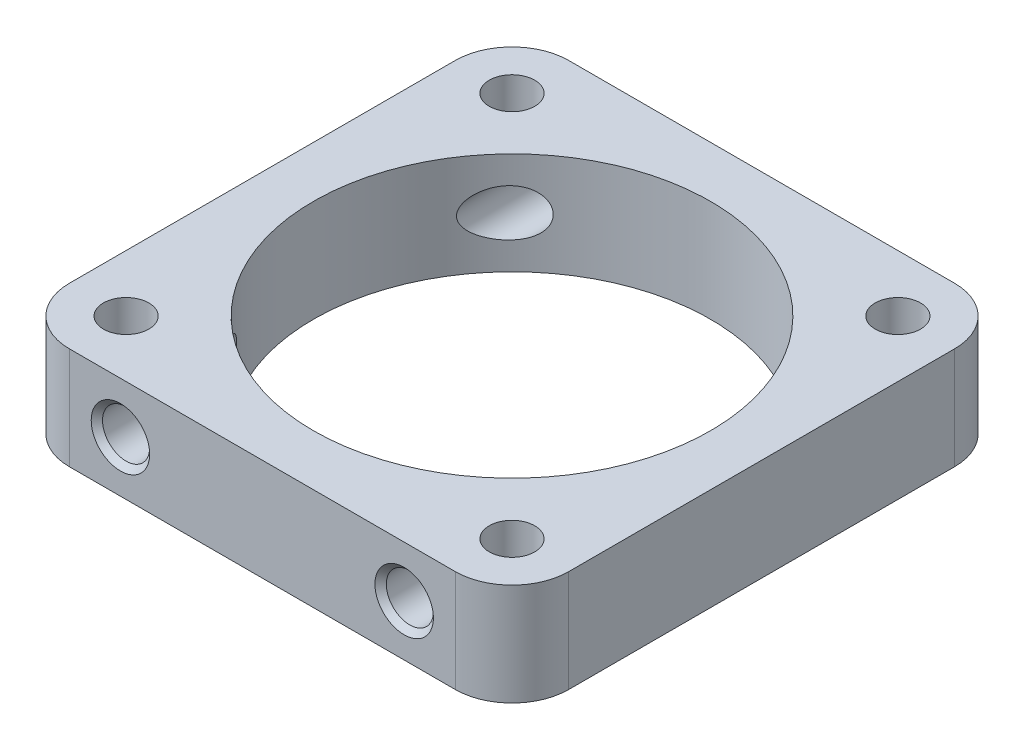
SolidWorks part; units mm, degrees
ref_plane "Front Plane" through (0, 0, 0) normal (0, 0, 1) x (1, 0, 0)
ref_plane "Top Plane" through (0, 0, 0) normal (0, 1, 0) x (1, 0, 0)
ref_plane "Right Plane" through (0, 0, 0) normal (1, 0, 0) x (0, 0, -1)
sketch "Sketch1" plane through (0, 0, 0) normal (0, 1, 0) x (1, 0, 0)
  line L1 (-44, -44) -> (44, -44)
  line L2 (-44, -44) -> (-44, 44)
  line L3 (-44, 44) -> (44, 44)
  line L4 (44, -44) -> (44, 44)
  line L5 (-44, -44) -> (44, 44) construction
  line L6 (-44, 44) -> (44, -44) construction
  point P0 (0, 0)
  dimension "D1" = 88
extrude "Boss-Extrude1" add sketch "Sketch1" along normal blind 18 contours L2 L1 L4 L3
fillet "Fillet1" radius 10 4 edges at (-44, 9, -44) (44, 9, -44) (44, 9, 44) (-44, 9, 44)
sketch "Sketch2" plane through (0, 18, 0) normal (0, 1, 0) x (1, 0, 0)
  circle A0 centre (-34, 34) radius 2.15
  circle A1 centre (34, 34) radius 2.15
  circle A2 centre (34, -34) radius 2.15
  circle A3 centre (-34, -34) radius 2.15
  dimension "D1" = 4.3
extrude "Cut-Extrude1" cut sketch "Sketch2" against normal through all
sketch "Sketch3" plane through (0, 0, 44) normal (0, 0, 1) x (1, 0, 0)
  line L0 (-34, 18) -> (-34, 0) construction
  line L1 (0, -1000) -> (0, 49000) construction
  line L2 (-1034, 9) -> (48966, 9) construction
  circle A0 centre (-25, 9) radius 4.15
  circle A1 centre (25, 9) radius 4.15
  point P4 (-34, 9)
  point P11 (0, 0)
  point P13 (0, 0)
  dimension "D1" = 8.3
  dimension "D2" = 50
extrude "Cut-Extrude2" cut sketch "Sketch3" against normal through all
sketch "Sketch4" plane through (0, 18, 0) normal (0, 1, 0) x (1, 0, 0)
  circle A0 centre (0, 0) radius 35
  dimension "D1" = 70
extrude "Cut-Extrude3" cut sketch "Sketch4" against normal through all
chamfer "Chamfer1" distance 1 angle 45 4 edges at (-20.85, 9, -44) (29.15, 9, -44) (-20.85, 9, 44) (29.15, 9, 44)
sketch "Sketch5" plane through (0, 18, 0) normal (0, 1, 0) x (1, 0, 0)
  circle A0 centre (-34, 34) radius 4
  circle A1 centre (34, 34) radius 4
  circle A2 centre (34, -34) radius 4
  circle A3 centre (-34, -34) radius 4
  dimension "D1" = 8
extrude "Cut-Extrude4" cut sketch "Sketch5" against normal offset from surface (13 mm away) 5 up to face at (0, 0, 35)
